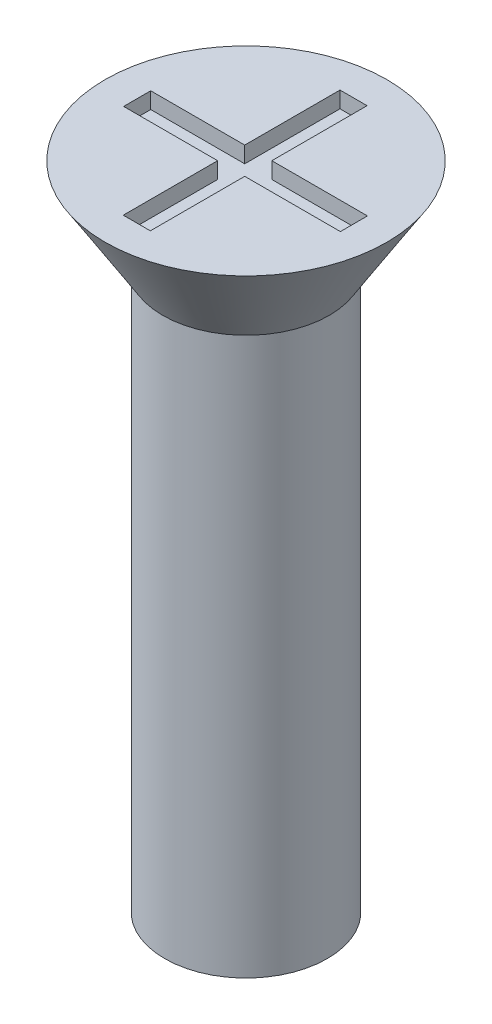
SolidWorks part; units mm, degrees
material "AISI 304"
ref_plane "Front" through (0, 0, 0) normal (0, 0, 1) x (1, 0, 0)
ref_plane "Top" through (0, 0, 0) normal (0, 1, 0) x (1, 0, 0)
ref_plane "Right" through (0, 0, 0) normal (1, 0, 0) x (0, 0, -1)
sketch "Sketch1" plane through (0, 0, 0) normal (0, 1, 0) x (1, 0, 0)
  circle A0 centre (0, 0) radius 1.5
  dimension "D1" = 3
extrude "Boss-Extrude1" add sketch "Sketch1" along normal blind 12
sketch "Sketch2" plane through (0, 12, 0) normal (0, 1, 0) x (1, 0, 0)
  circle A0 centre (0, 0) radius 2.6
  dimension "D1" = 5.2
extrude "Boss-Extrude2" add sketch "Sketch2" against normal blind 1.7 draft 32
sketch "Sketch3" plane through (0, 12, 0) normal (0, 1, 0) x (1, 0, 0)
  line L1 (-2, 0.2416) -> (2, 0.2416)
  line L2 (-2, 0.2416) -> (-2, -0.2584)
  line L3 (-2, -0.2584) -> (2, -0.2584)
  line L4 (2, 0.2416) -> (2, -0.2584)
  line L5 (-0.2653, 2) -> (0.2347, 2)
  line L6 (-0.2653, 2) -> (-0.2653, -2)
  line L7 (-0.2653, -2) -> (0.2347, -2)
  line L8 (0.2347, 2) -> (0.2347, -2)
  circle A0 centre (0, 0) radius 2.6 construction
  dimension "D1" = 0.5
  dimension "D2" = 0.5
  dimension "D3" = 4
  dimension "D4" = 4
  dimension "D5" = 2
  dimension "D6" = 2
extrude "Cut-Extrude1" cut sketch "Sketch3" against normal blind 0.3 contours L8 L5 L6 L1 | L8 L3 L6 L7 | L6 L1 L2 L3 | L1 L8 L3 L4 | L8 L1 L6 L3
